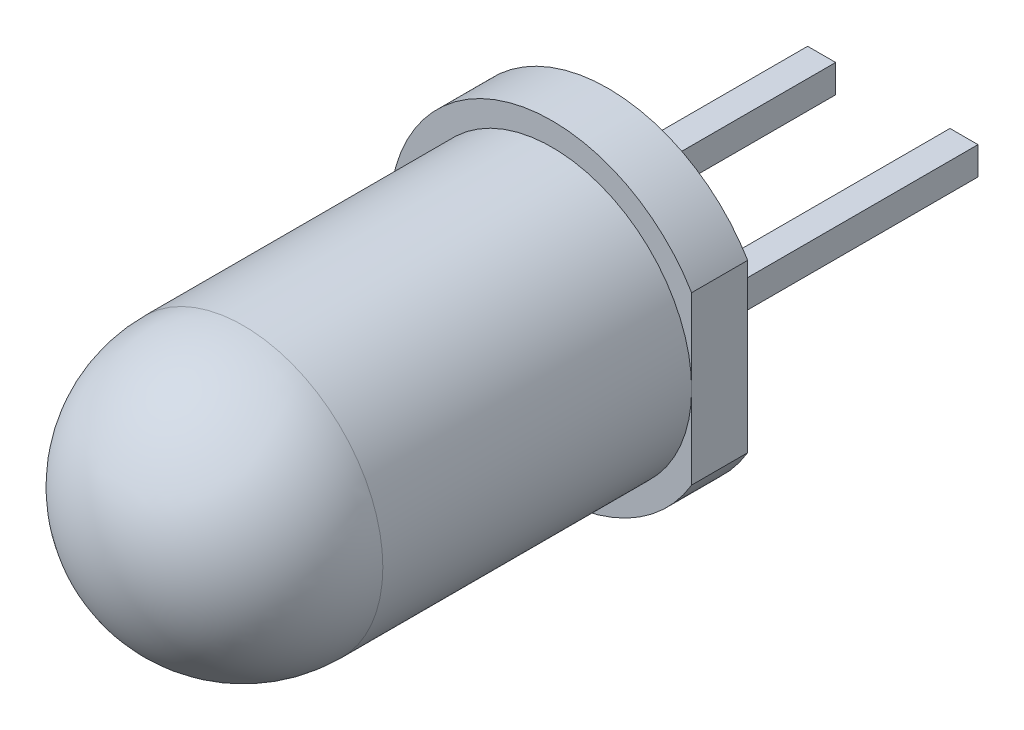
SolidWorks part; units mm, degrees
ref_plane "Front" through (0, 0, 0) normal (0, 0, 1) x (1, 0, 0)
ref_plane "Top" through (0, 0, 0) normal (0, 1, 0) x (1, 0, 0)
ref_plane "Right" through (0, 0, 0) normal (1, 0, 0) x (0, 0, -1)
sketch "Sketch1" plane through (0, 0, 0) normal (0, 1, 0) x (1, 0, 0)
  line L0 (0, -2.49) -> (0, 6.51) construction
  line L1 (-2.49, 0) -> (-2.49, 6.51)
  line L2 (-2.49, 6.51) -> (0, 6.51)
  line L3 (0, 6.51) -> (0, -2.49)
  arc A0 (-2.49, 0) -> (0, -2.49) centre (0, 0) ccw
  point P3 (0, -2.49)
  dimension "D1" = 2.49
  dimension "D2" = 9
revolve "Revolve1" add sketch "Sketch1" angle 360 about L0
sketch "Sketch2" plane through (0, 0, -6.51) normal (0, 0, -1) x (-1, 0, 0)
  line L0 (-2.49, 1.4866) -> (-2.49, -1.4866)
  arc A0 (-2.49, -1.4866) -> (-2.49, 1.4866) centre (0, 0) ccw
  circle A1 centre (0, 0) radius 2.49 construction
  dimension "D1" = 5.8
extrude "Boss-Extrude1" add sketch "Sketch2" against normal blind 1
sketch "Sketch3" plane through (0, 0, -6.51) normal (0, 0, -1) x (-1, 0, 0)
  line L0 (-1.27, 0) -> (1.27, 0) construction
  line L1 (-1.52, -0.25) -> (-1.02, -0.25)
  line L2 (-1.52, -0.25) -> (-1.52, 0.25)
  line L3 (-1.52, 0.25) -> (-1.02, 0.25)
  line L4 (-1.02, -0.25) -> (-1.02, 0.25)
  line L5 (-1.52, -0.25) -> (-1.02, 0.25) construction
  line L6 (-1.52, 0.25) -> (-1.02, -0.25) construction
  line L7 (1.02, -0.25) -> (1.52, -0.25)
  line L8 (1.02, -0.25) -> (1.02, 0.25)
  line L9 (1.02, 0.25) -> (1.52, 0.25)
  line L10 (1.52, -0.25) -> (1.52, 0.25)
  line L11 (1.02, -0.25) -> (1.52, 0.25) construction
  line L12 (1.02, 0.25) -> (1.52, -0.25) construction
  point P0 (-1.27, 0)
  point P5 (1.27, 0)
  dimension "D1" = 0.5
  dimension "D2" = 0.5
  dimension "D3" = 2.54
extrude "Boss-Extrude2" add sketch "Sketch3" along normal blind 5.08 separate body
